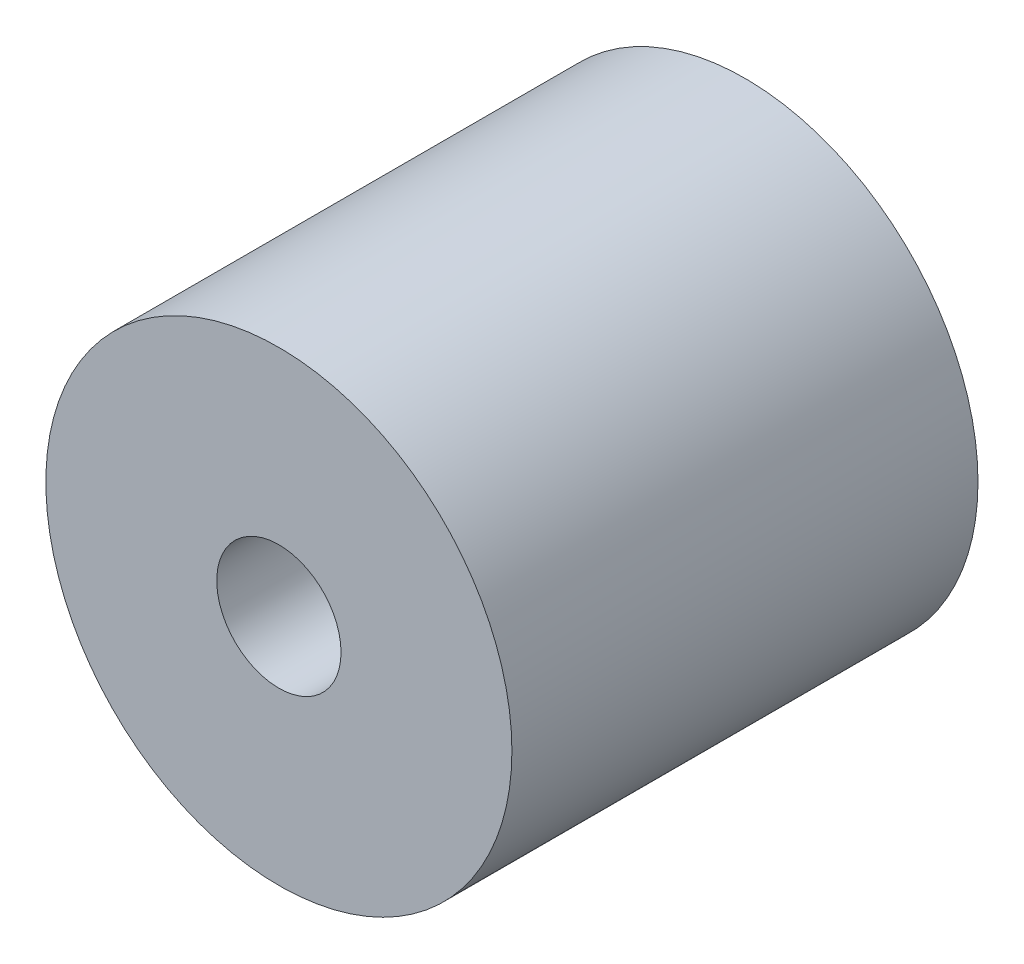
SolidWorks part; units mm, degrees
ref_plane "Alzado" through (0, 0, 0) normal (0, 0, 1) x (1, 0, 0)
ref_plane "Planta" through (0, 0, 0) normal (0, 1, 0) x (1, 0, 0)
ref_plane "Vista lateral" through (0, 0, 0) normal (1, 0, 0) x (0, 0, -1)
sketch "Croquis1" plane through (0, 0, 0) normal (0, 0, 1) x (1, 0, 0)
  circle A0 centre (0, 0) radius 150
  circle A1 centre (0, 0) radius 40
  dimension "D1" = 300
  dimension "D2" = 80
extrude "Saliente-Extruir1" add sketch "Croquis1" along normal blind 300
